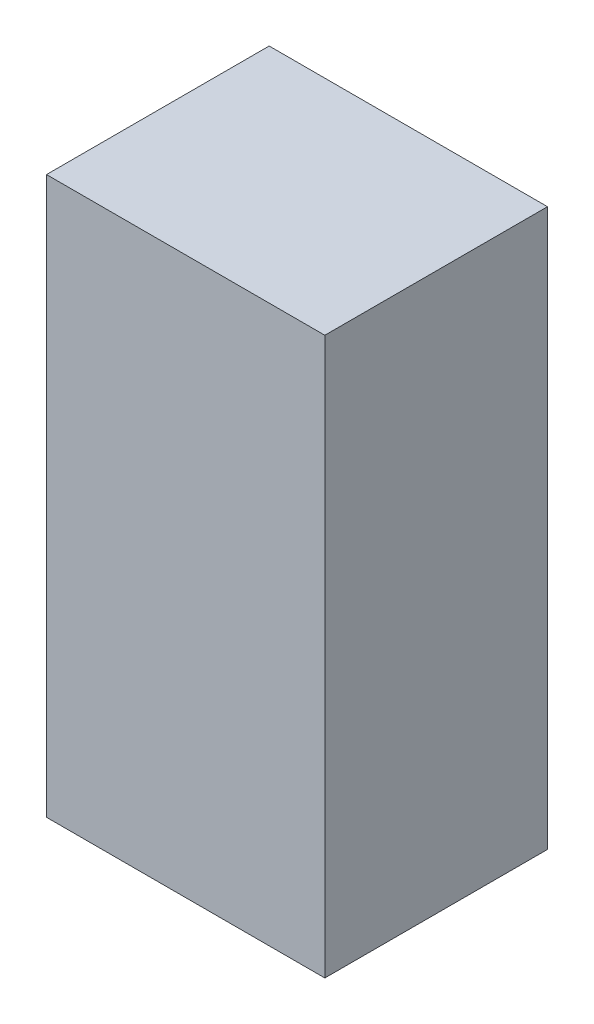
SolidWorks part; units mm, degrees
ref_plane "Front Plane" through (0, 0, 0) normal (0, 0, 1) x (1, 0, 0)
ref_plane "Top Plane" through (0, 0, 0) normal (0, 1, 0) x (1, 0, 0)
ref_plane "Right Plane" through (0, 0, 0) normal (1, 0, 0) x (0, 0, -1)
sketch "Sketch1" plane through (0, 0, 0) normal (0, 1, 0) x (1, 0, 0)
  line L1 (0, 0) -> (0.75, 0)
  line L2 (0, 0) -> (0, 0.6)
  line L3 (0, 0.6) -> (0.75, 0.6)
  line L4 (0.75, 0) -> (0.75, 0.6)
  dimension "D1" = 0.6
  dimension "D2" = 0.75
extrude "Boss-Extrude1" add sketch "Sketch1" along normal blind 1.5
scale "Scale1" scale about centroid uniform scaling yes scale factor 10
